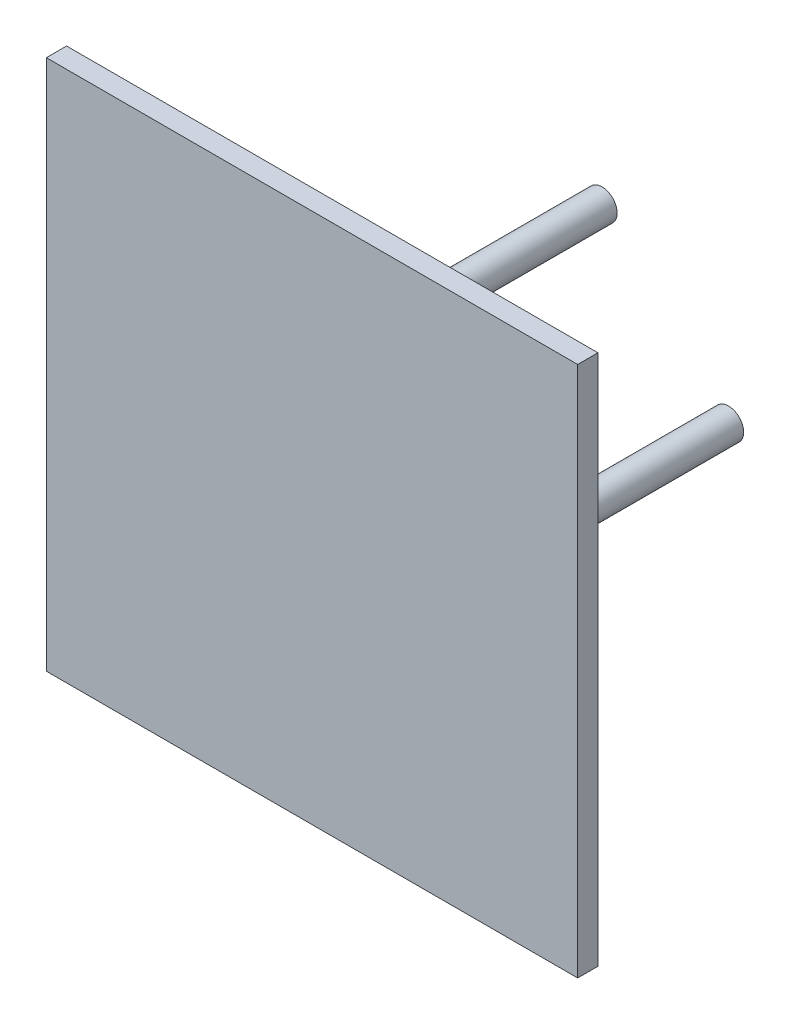
SolidWorks part; units mm, degrees
ref_plane "前视基准面" through (0, 0, 0) normal (0, 0, 1) x (1, 0, 0)
ref_plane "上视基准面" through (0, 0, 0) normal (0, 1, 0) x (1, 0, 0)
ref_plane "右视基准面" through (0, 0, 0) normal (1, 0, 0) x (0, 0, -1)
other "Configuration Table"
sketch "Sketch1" plane through (0, 0, 0) normal (0, 0, 1) x (1, 0, 0)
  line L1 (0, 0) -> (105, 0)
  line L2 (0, 0) -> (0, 105)
  line L3 (0, 105) -> (105, 105)
  line L4 (105, 0) -> (105, 105)
  dimension "D1" = 105
  dimension "D2" = 105
extrude "Boss-Extrude1" add sketch "Sketch1" along normal blind 4
sketch "Sketch2" plane through (0, 0, 0) normal (0, 0, -1) x (-1, 0, 0)
  line L0 (0, 0) -> (-105, 0) construction
  line L1 (-105, 0) -> (-105, 105) construction
  circle A0 centre (-52.5, 52.5) radius 3
  dimension "D2" = 52.5
  dimension "D3" = 6
  dimension "D1" = 52.5
extrude "Cut-Extrude1" cut sketch "Sketch2" against normal blind 2
sketch "Sketch3" plane through (0, 0, 0) normal (0, 0, -1) x (-1, 0, 0)
  line L0 (0, 105) -> (0, 0) construction
  line L1 (-105, 105) -> (0, 105) construction
  line L3 (-46.5, 55) -> (-40, 55)
  line L5 (-49.4406, 53) -> (-40, 53)
  line L6 (-40, 55) -> (-40, 53)
  line L7 (-46.5, 50) -> (-40, 50)
  line L9 (-49.4406, 52) -> (-40, 52)
  line L10 (-40, 50) -> (-40, 52)
  arc A1 (-49.4406, 53) -> (-49.4406, 52) centre (-52.5, 52.5) ccw
  arc A2 (-46.5, 55) -> (-46.5, 50) centre (-52.5, 52.5) ccw
  dimension "D1" = 13
  dimension "D2" = 6.2
  dimension "D3" = 52.5
  dimension "D4" = 52.5
  dimension "D5" = 1
  dimension "D6" = 2
  dimension "D7" = 40
  dimension "D8" = 40
  dimension "D9" = 46.5
  dimension "D10" = 46.5
  dimension "D11" = 55
extrude "Boss-Extrude5" add sketch "Sketch3" along normal blind 12
sketch "Sketch4" plane through (0, 55, 0) normal (0, 1, 0) x (1, 0, 0)
  line L0 (40, 12) -> (46.5, 12) construction
  line L1 (40, 12) -> (40, 0) construction
  circle A0 centre (43.25, 6) radius 1.9987
  point P4 (43.25, 12)
  point P8 (40, 6)
  dimension "D1" = 3.9974
extrude "Cut-Extrude2" cut sketch "Sketch4" against normal blind 12
fillet "Fillet1" radius 1 2 edges at (40, 51, -12) (40, 54, -12)
sketch "Sketch5" plane through (0, 0, 0) normal (0, 0, -1) x (-1, 0, 0)
  circle A0 centre (-52.5, 77.5) radius 3
  arc A1 (-49.4406, 53) -> (-49.4406, 52) centre (-52.5, 52.5) ccw construction
  circle A2 centre (-52.5, 52.5) radius 3 construction
  circle A4 centre (-27.5, 52.5) radius 3
  circle A5 centre (-52.5, 27.5) radius 3
  circle A6 centre (-77.5, 52.5) radius 3
  point P5 (0, 0)
  point P17 (-52.5, 52.5)
  dimension "D1" = 6
  dimension "D2" = 25
  dimension "D3" = 4
extrude "Boss-Extrude7" add sketch "Sketch5" along normal blind 53.3
